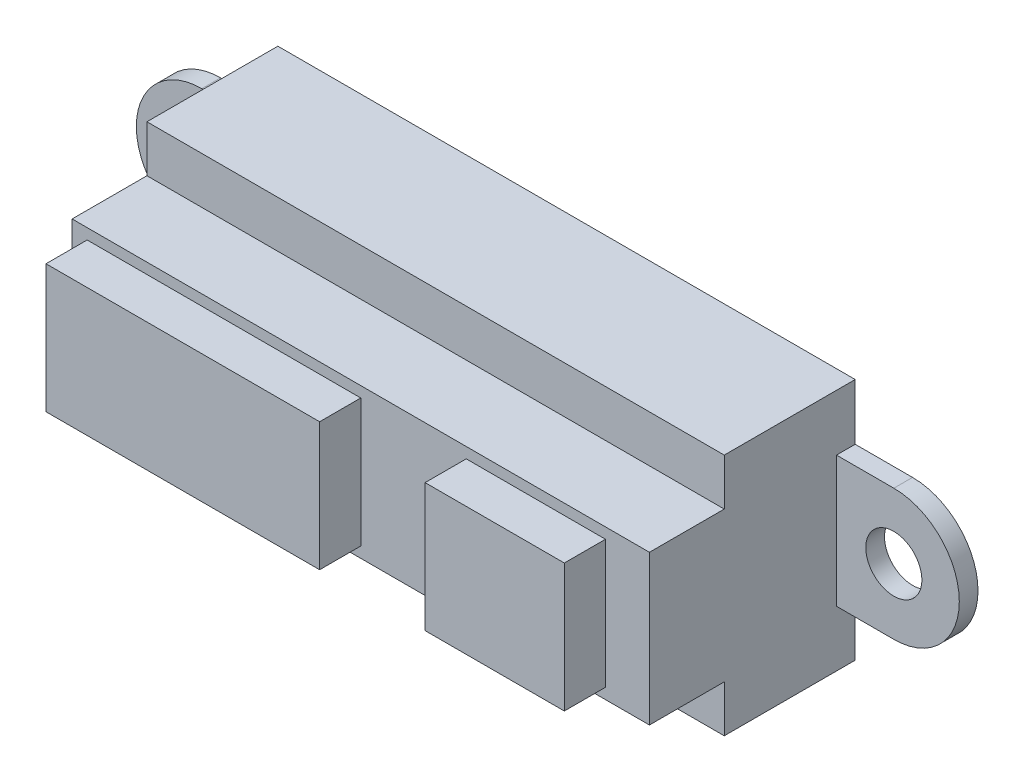
SolidWorks part; units mm, degrees
ref_plane "前视基准面" through (0, 0, 0) normal (0, 0, 1) x (1, 0, 0)
ref_plane "上视基准面" through (0, 0, 0) normal (0, 1, 0) x (1, 0, 0)
ref_plane "右视基准面" through (0, 0, 0) normal (1, 0, 0) x (0, 0, -1)
sketch "草图1" plane through (0, 0, 0) normal (0, 0, 1) x (1, 0, 0)
  line L0 (-36.7762, 0) -> (0, 0) construction
  line L1 (-18.5, 3.5) -> (18.5, 3.5)
  line L2 (-18.5, 3.5) -> (-18.5, -3.5)
  line L3 (-18.5, -3.5) -> (18.5, -3.5)
  line L4 (18.5, 3.5) -> (18.5, -3.5)
  line L5 (0, 0) -> (0, 29.0181) construction
  dimension "D1" = 37
  dimension "D2" = 7
extrude "凸台-拉伸1" add sketch "草图1" along normal blind 1
sketch "草图3" plane through (0, 0, 0) normal (0, 0, 1) x (1, 0, 0)
  line L2 (-15.4335, 6.5) -> (-15.4335, -6.5)
  line L3 (-15.4335, -6.5) -> (15.4335, -6.5)
  line L4 (15.4335, 6.5) -> (15.4335, -6.5)
  line L6 (0, 0) -> (0, -24.9943) construction
  line L7 (-15.4335, 6.5) -> (15.4335, 6.5)
  line L8 (0, 0) -> (27.1081, 0) construction
  dimension "D1" = 30.867
  dimension "D2" = 13
extrude "凸台-拉伸2" add sketch "草图3" along normal blind 7
sketch "草图4" plane through (0, 0, 0) normal (0, 0, 1) x (1, 0, 0)
  line L0 (-15.4335, -3.5) -> (-15.4335, 3.5) construction
  line L1 (-15.4335, 4) -> (15.4335, 4)
  line L2 (-15.4335, 4) -> (-15.4335, -4)
  line L3 (-15.4335, -4) -> (15.4335, -4)
  line L4 (15.4335, 4) -> (15.4335, -4)
  line L5 (15.4335, -6.5) -> (15.4335, 6.5) construction
  line L6 (0, 0) -> (35.9525, 0) construction
  dimension "D1" = 8
extrude "凸台-拉伸3" add sketch "草图4" along normal blind 11
sketch "草图5" plane through (0, 0, 0) normal (0, 0, 1) x (1, 0, 0)
  line L1 (-14.6301, 3.4272) -> (0, 3.4272)
  line L2 (-14.6301, 3.4272) -> (-14.6301, -3.4272)
  line L3 (-14.6301, -3.4272) -> (0, -3.4272)
  line L4 (0, 3.4272) -> (0, -3.4272)
  line L5 (5.6383, 3.4272) -> (13.0824, 3.4272)
  line L6 (5.6383, 3.4272) -> (5.6383, -3.4272)
  line L7 (5.6383, -3.4272) -> (13.0824, -3.4272)
  line L8 (13.0824, 3.4272) -> (13.0824, -3.4272)
extrude "凸台-拉伸4" add sketch "草图5" along normal blind 13.2
sketch "草图6" plane through (0, 0, 1) normal (0, 0, 1) x (1, 0, 0)
  line L0 (18.5, -3.5) -> (18.5, 3.5) construction
  line L1 (-18.5, 3.5) -> (-18.5, -3.5) construction
  circle A0 centre (18.5, 0) radius 3.5
  circle A1 centre (-18.5, 0) radius 3.5
extrude "凸台-拉伸5" add sketch "草图6" against normal up to surface (1 mm away) up to face at (0, 0, 0)
hole_wizard "Ø3.0 (3) 直径孔1" positions "草图7" profile "草图8" hole size "Ø3.0" standard "GB"
sketch "草图7" plane through (0, 0, 1) normal (0, 0, 1) x (1, 0, 0)
  point P0 (-18.5, 0)
  point P3 (18.5, 0)
sketch "草图8" plane through (-18.5, 0, 1) normal (1, 0, 0) x (0, -1, 0)
  line L0 (0, 0) -> (0, 9.4013)
  line L1 (0, 9.4013) -> (1.5, 8.5)
  line L2 (1.5, 8.5) -> (1.5, 0)
  line L5 (1.5, 0) -> (0, 0)
  line L10 (0, 9.4013) -> (-1.5, 8.5) construction
  line L11 (0, -6.35) -> (0, 107.95) construction
  dimension "孔直径" = 3
  dimension "孔深度" = 8.5
  dimension "导头角度" = 118
